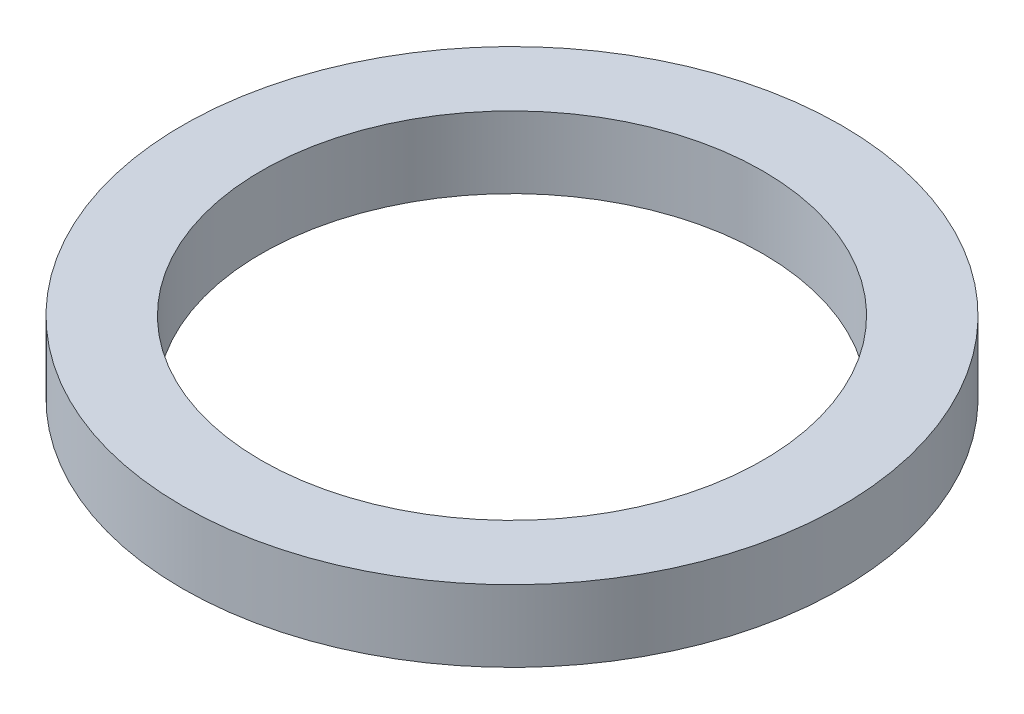
SolidWorks part; units mm, degrees
ref_plane "Front Plane" through (0, 0, 0) normal (0, 0, 1) x (1, 0, 0)
ref_plane "Top Plane" through (0, 0, 0) normal (0, 1, 0) x (1, 0, 0)
ref_plane "Right Plane" through (0, 0, 0) normal (1, 0, 0) x (0, 0, -1)
sketch "Sketch1" plane through (0, 0, 0) normal (0, 1, 0) x (1, 0, 0)
  circle A0 centre (0, 0) radius 2.3
  dimension "D1" = 4.6
extrude "Boss-Extrude1" add sketch "Sketch1" along normal blind 0.5
sketch "Sketch2" plane through (0, 0.5, 0) normal (0, 1, 0) x (1, 0, 0)
  circle A0 centre (0, 0) radius 1.75
  dimension "D1" = 3.5
extrude "Cut-Extrude1" cut sketch "Sketch2" against normal through all
